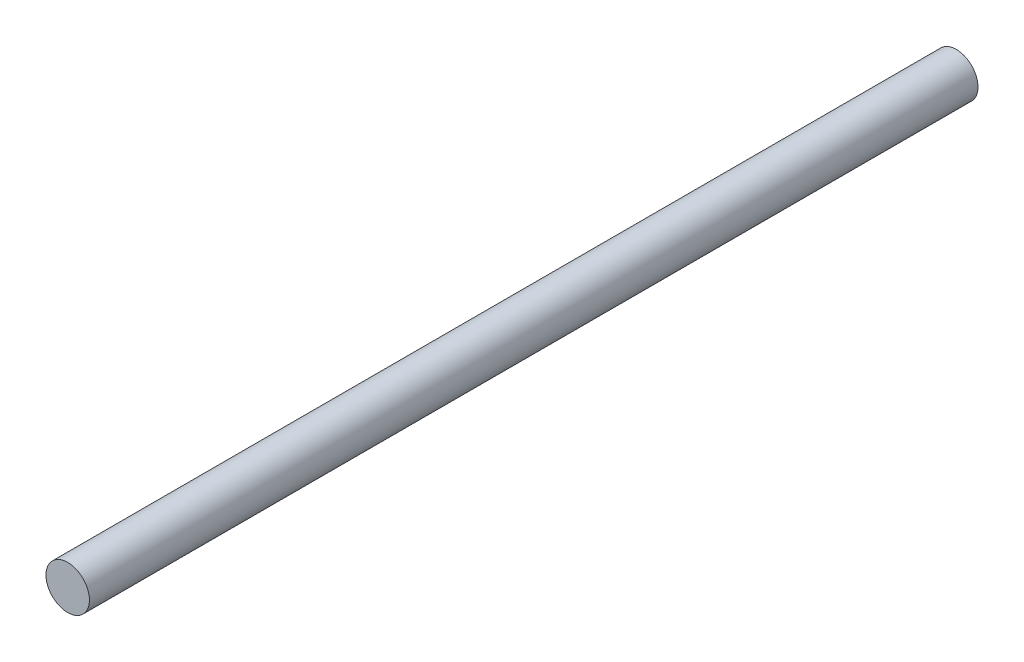
SolidWorks part; units mm, degrees
ref_plane "Front Plane" through (0, 0, 0) normal (0, 0, 1) x (1, 0, 0)
ref_plane "Top Plane" through (0, 0, 0) normal (0, 1, 0) x (1, 0, 0)
ref_plane "Right Plane" through (0, 0, 0) normal (1, 0, 0) x (0, 0, -1)
sketch "Sketch1" plane through (0, 0, 0) normal (0, 0, 1) x (1, 0, 0)
  circle A0 centre (0, 0) radius 4
  dimension "D1" = 8
extrude "Boss-Extrude1" add sketch "Sketch1" along normal blind 163.5
move or copy body "Body-Move/Copy1" [suppressed] bodies to move or copy 101
